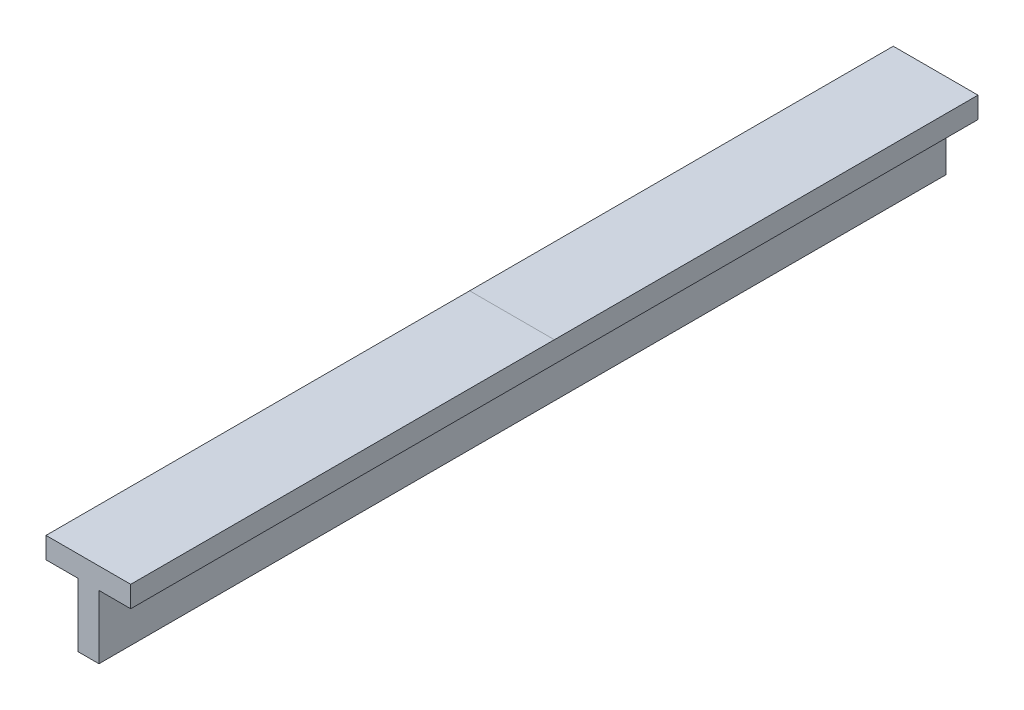
SolidWorks part; units mm, degrees
ref_plane "Front Plane" through (0, 0, 0) normal (0, 0, 1) x (1, 0, 0)
ref_plane "Top Plane" through (0, 0, 0) normal (0, 1, 0) x (1, 0, 0)
ref_plane "Right Plane" through (0, 0, 0) normal (1, 0, 0) x (0, 0, -1)
sketch "Szkic1" plane through (0, 0, 0) normal (0, 0, 1) x (1, 0, 0)
  line L0 (0, 0) -> (50, 0)
  line L1 (50, 0) -> (50, 150)
  line L2 (50, 150) -> (125, 150)
  line L3 (125, 150) -> (125, 200)
  line L4 (125, 200) -> (-75, 200)
  line L5 (-75, 200) -> (-75, 150)
  line L6 (-75, 150) -> (0, 150)
  line L7 (0, 150) -> (0, 0)
  point P3 (25, 200)
  point P10 (25, 0)
  dimension "D1" = 50
  dimension "D2" = 50
  dimension "D3" = 200
  dimension "D4" = 200
extrude "Dodanie-wyciągnięcie1" add sketch "Szkic1" along normal blind 2000
sketch "Szkic2" plane through (0, 200, 0) normal (0, 1, 0) x (1, 0, 0)
  line L0 (-75, -1000) -> (125, -1000)
  line L1 (-75, -2000) -> (-75, 0) construction
  line L2 (125, -2000) -> (125, 0) construction
  line L3 (125, 0) -> (-75, 0) construction
  dimension "D1" = 1000
split line "Linia podziałowa1"
